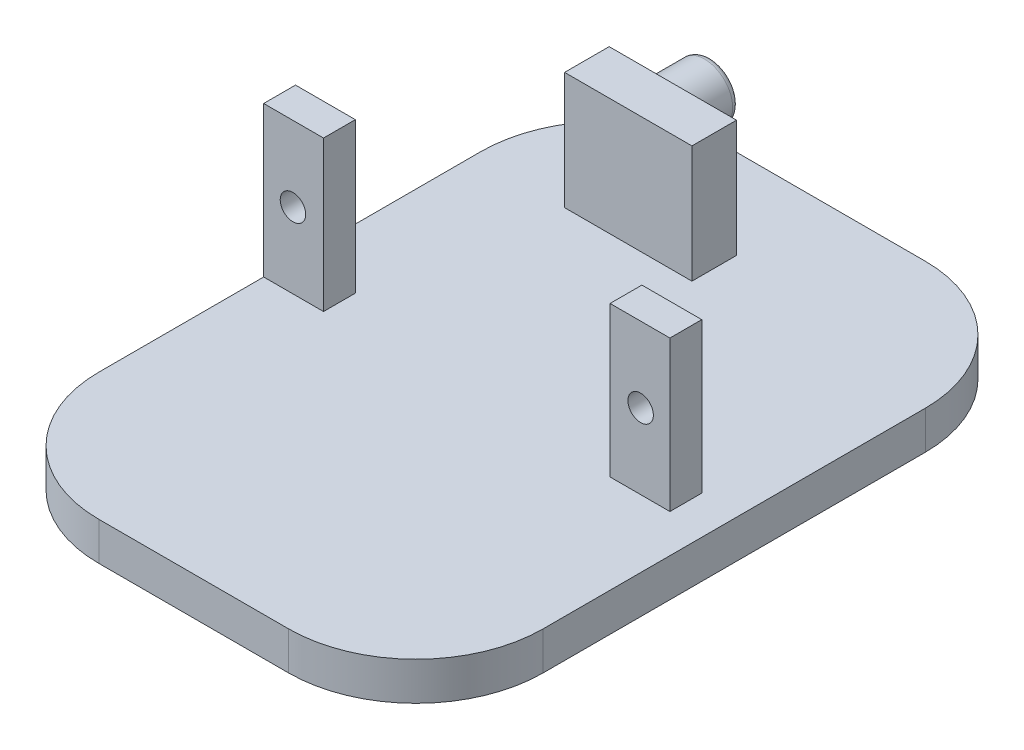
SolidWorks part; units mm, degrees
ref_plane "Plan de face" through (0, 0, 0) normal (0, 0, 1) x (1, 0, 0)
ref_plane "Plan de dessus" through (0, 0, 0) normal (0, 1, 0) x (1, 0, 0)
ref_plane "Plan de droite" through (0, 0, 0) normal (1, 0, 0) x (0, 0, -1)
sketch "Esquisse1" plane through (0, 0, 0) normal (0, 0, 1) x (1, 0, 0)
  line L1 (0, 0) -> (34.9, 0)
  line L2 (0, 0) -> (0, 3)
  line L3 (0, 3) -> (34.9, 3)
  line L4 (34.9, 0) -> (34.9, 3)
  dimension "D1" = 3
  dimension "D2" = 34.9
extrude "Boss.-Extru.1" add sketch "Esquisse1" along normal blind 50
sketch "Esquisse2" plane through (0, 3, 0) normal (0, 1, 0) x (1, 0, 0)
  line L0 (17.45, 0) -> (17.45, -50) construction
  line L1 (34.9, 0) -> (0, 0) construction
  line L2 (34.9, -50) -> (0, -50) construction
  line L3 (31.9, -50) -> (31.9, 0) construction
  line L4 (3, -50) -> (3, 0) construction
  line L5 (31.9, -25) -> (3, -25) construction
  line L7 (17.1, -10.52) -> (7.1, -10.52)
  line L12 (17.1, -10.52) -> (17.1, -7.02)
  line L13 (17.1, -7.02) -> (7.1, -7.02)
  line L14 (7.1, -10.52) -> (7.1, -7.02)
  dimension "D1" = 3
  dimension "D2" = 10.52
  dimension "D3" = 10
  dimension "D4" = 3.5
  dimension "D5" = 0.35
extrude "Boss.-Extru.2" add sketch "Esquisse2" along normal blind 9.2 contours L7 L14 L13 L12
sketch "Esquisse3" plane through (0, 0, 7.02) normal (0, 0, -1) x (-1, 0, 0)
  circle A0 centre (-10.6, 8.9) radius 2.2
  dimension "D1" = 4.4
extrude "Boss.-Extru.3" add sketch "Esquisse3" along normal up to surface (4.5 mm away)
fillet "Congé1" radius 0.5 1 edges at (10.6, 11.1, 2.52)
sketch "Esquisse5" plane through (0, 3, 0) normal (0, 1, 0) x (1, 0, 0)
  line L0 (15.95, -50) -> (15.95, 0) construction
  line L1 (27.2, -27.05) -> (31.9, -27.05)
  line L2 (27.2, -27.05) -> (27.2, -24.55)
  line L3 (27.2, -24.55) -> (31.9, -24.55)
  line L4 (31.9, -27.05) -> (31.9, -24.55)
  line L7 (4.7, -24.55) -> (0, -24.55)
  line L8 (0, -27.05) -> (0, -24.55)
  line L9 (4.7, -27.05) -> (0, -27.05)
  line L10 (4.7, -27.05) -> (4.7, -24.55)
  line L11 (31.9, -27.05) -> (27.2, -27.05) construction
  line L13 (0, -50) -> (0, 0) construction
  dimension "D1" = 4.7
  dimension "D2" = 2.5
  dimension "D3" = 22.5
extrude "Boss.-Extru.5" add sketch "Esquisse5" along normal up to surface (11.8 mm away) contours L7 L8 L9 L10 | L3 L4 L1 L2
sketch "Esquisse6" plane through (0, 0, 27.05) normal (0, 0, 1) x (1, 0, 0)
  circle A0 centre (29.6, 8.9) radius 1
  circle A1 centre (2.3, 8.9) radius 1
  dimension "D1" = 2
  dimension "D2" = 2
extrude "Enlèv. mat.-Extru.1" cut sketch "Esquisse6" against normal up to next
fillet "Congé2" radius 10 4 edges at (34.9, 1.5, 50) (34.9, 1.5, 0) (0, 1.5, 0) (0, 1.5, 50)
